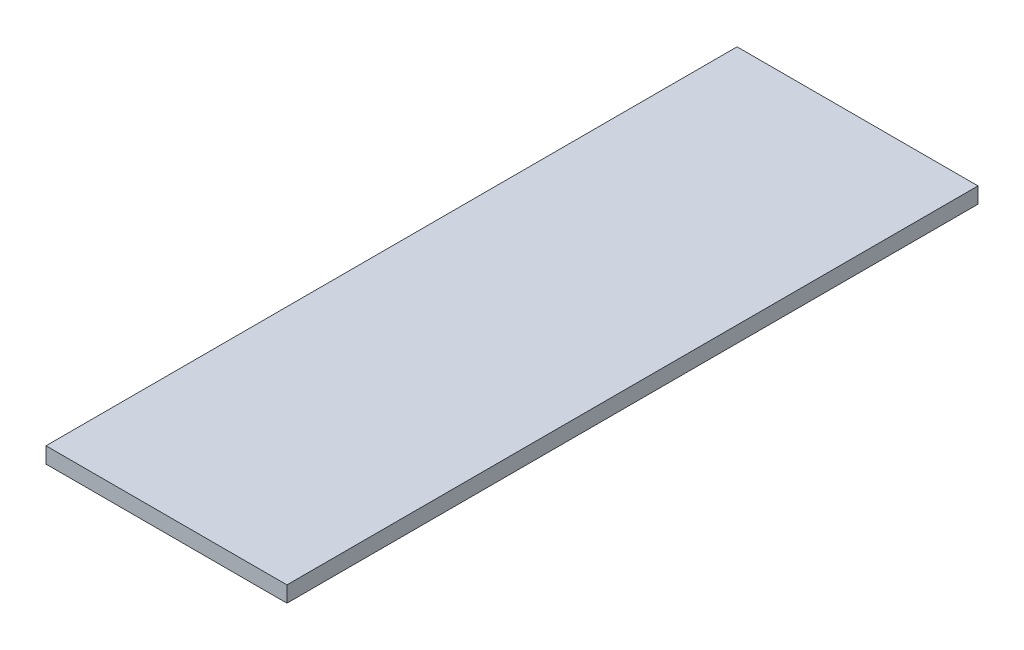
SolidWorks part; units mm, degrees
material "Silicon Rubber"
ref_plane "Front" through (0, 0, 0) normal (0, 0, 1) x (1, 0, 0)
ref_plane "Top" through (0, 0, 0) normal (0, 1, 0) x (1, 0, 0)
ref_plane "Right" through (0, 0, 0) normal (1, 0, 0) x (0, 0, -1)
sketch "Sketch1" plane through (0, 0, 0) normal (0, 1, 0) x (1, 0, 0)
  line L0 (-22.5, -67.5) -> (22.5, -67.5) construction
  line L1 (-24.0875, -69.0875) -> (24.0875, -69.0875)
  line L2 (-24.0875, -69.0875) -> (-24.0875, 69.0875)
  line L3 (-24.0875, 69.0875) -> (24.0875, 69.0875)
  line L4 (24.0875, -69.0875) -> (24.0875, 69.0875)
  line L5 (-24.0875, -69.0875) -> (24.0875, 69.0875) construction
  line L6 (-24.0875, 69.0875) -> (24.0875, -69.0875) construction
  line L7 (22.5, 67.5) -> (22.5, -67.5) construction
  point P0 (0, 0)
  dimension "D1" = 1.5875
  dimension "D2" = 1.5875
extrude "Boss-Extrude1" add sketch "Sketch1" along normal blind 3.175
